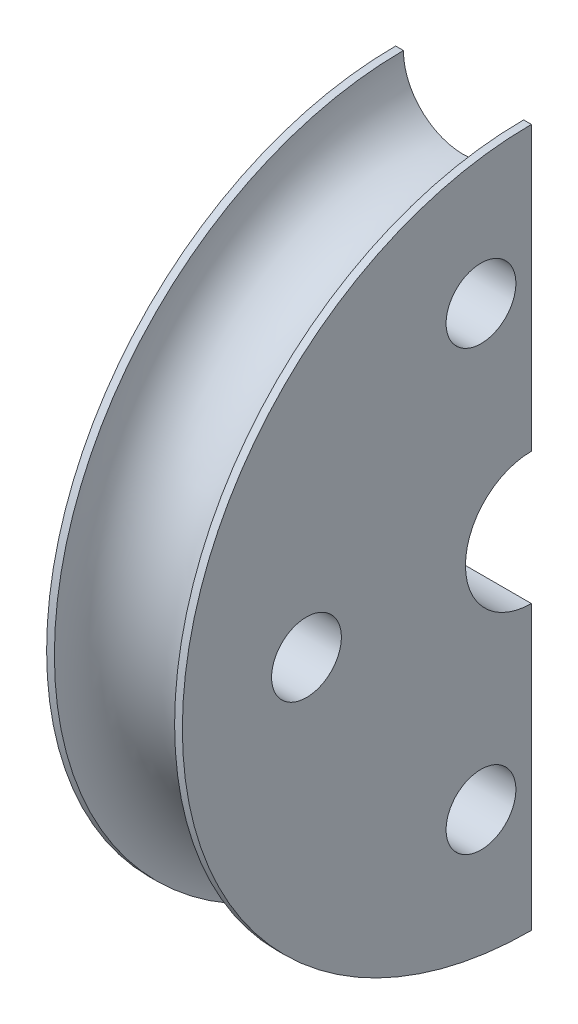
SolidWorks part; units mm, degrees
material "Acier allié"
ref_plane "Plan de face" through (0, 0, 0) normal (0, 0, 1) x (1, 0, 0)
ref_plane "Plan de dessus" through (0, 0, 0) normal (0, 1, 0) x (1, 0, 0)
ref_plane "Plan de droite" through (0, 0, 0) normal (1, 0, 0) x (0, 0, -1)
sketch "Esquisse1" plane through (0, 0, 0) normal (0, 0, 1) x (1, 0, 0)
  line L0 (0, 0) -> (75.7163, 0) construction
  line L1 (0, 17) -> (0, 90)
  line L2 (0, 90) -> (2, 90)
  line L3 (35, 90) -> (35, 17)
  line L4 (35, 90) -> (33, 90)
  line L5 (0, 17) -> (35, 17)
  arc A0 (2, 90) -> (33, 90) centre (17.5, 90) ccw
  dimension "D1" = 35
  dimension "D2" = 2
  dimension "D3" = 2
  dimension "D5" = 34
revolve "Révolution1" add sketch "Esquisse1" angle 180 about L0
sketch "Esquisse2" plane through (0, 0, 0) normal (-1, 0, 0) x (0, 0, 1)
  line L0 (0, -90) -> (0, -17) construction
  line L1 (0, 90) -> (0, 17) construction
  circle A0 centre (13, -56.5243) radius 9
  circle A1 centre (58, 0) radius 9
  circle A2 centre (13, 56.5243) radius 9
  dimension "D1" = 18
  dimension "D3" = 18
  dimension "D4" = 18
  dimension "D2" = 58
  dimension "D5" = 13
  dimension "D6" = 13
  dimension "D7" = 58
  dimension "D8" = 58
extrude "Enlèv. mat.-Extru.1" cut sketch "Esquisse2" against normal through all
